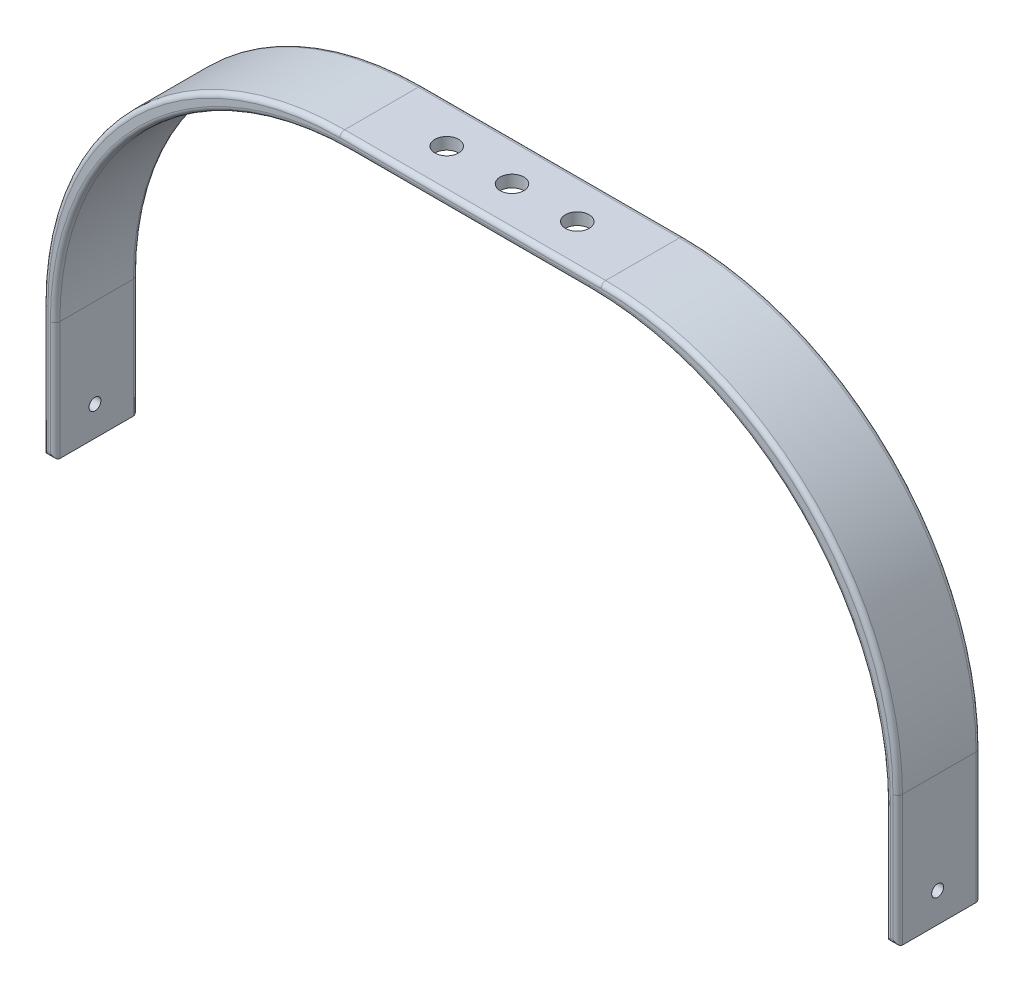
SolidWorks part; units mm, degrees
ref_plane "Front Plane" through (0, 0, 0) normal (0, 0, 1) x (1, 0, 0)
ref_plane "Top Plane" through (0, 0, 0) normal (0, 1, 0) x (1, 0, 0)
ref_plane "Right Plane" through (0, 0, 0) normal (1, 0, 0) x (0, 0, -1)
sketch "Sketch1" plane through (0, 0, 0) normal (0, 0, 1) x (1, 0, 0)
  line L0 (-110, 0) -> (90, 0)
  line L1 (340, -250) -> (340, -350)
  line L2 (-360, -250) -> (-360, -350)
  line L3 (-360, -350) -> (-370, -350)
  line L4 (-370, -350) -> (-370, -240)
  line L5 (-120, 10) -> (100, 10)
  line L6 (350, -240) -> (350, -350)
  line L7 (350, -350) -> (340, -350)
  arc A0 (100, 10) -> (350, -240) centre (100, -240) cw
  arc A1 (90, 0) -> (340, -250) centre (90, -250) cw
  arc A2 (-110, 0) -> (-360, -250) centre (-110, -250) ccw
  arc A3 (-370, -240) -> (-120, 10) centre (-120, -240) cw
  point P13 (340, 0)
  point P16 (-360, 0)
  dimension "D8" = 250
  dimension "D1" = 350
  dimension "D2" = 700
  dimension "D3" = 350
  dimension "D4" = 10
  dimension "D5" = 10
  dimension "D6" = 10
  dimension "D7" = 350
extrude "Boss-Extrude1" add sketch "Sketch1" along normal blind 70
sketch "Sketch2" plane through (350, 0, 0) normal (1, 0, 0) x (0, 0, -1)
  line L0 (-70, -350) -> (0, -350) construction
  circle A0 centre (-36.3899, -325) radius 5
  dimension "D1" = 10
  dimension "D2" = 25
extrude "Cut-Extrude1" cut sketch "Sketch2" against normal blind 816
sketch "Sketch3" plane through (0, 10, 0) normal (0, 1, 0) x (1, 0, 0)
  line L0 (-120, -35) -> (100, -35) construction
  line L1 (-120, -70) -> (-120, 0) construction
  line L2 (100, -70) -> (100, 0) construction
  circle A0 centre (-65, -35) radius 10
  circle A1 centre (-10, -35) radius 10
  circle A2 centre (45, -35) radius 10
  dimension "D1" = 20
  dimension "D2" = 55
  dimension "D3" = 3
extrude "Cut-Extrude2" cut sketch "Sketch3" against normal blind 143
fillet "Fillet1" radius 4 24 edges at (-10, 10, 0) (-296.7767, -63.2233, 0) (-370, -295, 0) (-365, -350, 0) (-360, -300, 0) (-286.7767, -73.2233, 0) (-10, 0, 0) (266.7767, -73.2233, 0) (340, -300, 0) (345, -350, 0) (350, -295, 0) (276.7767, -63.2233, 0) (350, -295, 70) (345, -350, 70) (340, -300, 70) (266.7767, -73.2233, 70) (-10, 0, 70) (-286.7767, -73.2233, 70) (-360, -300, 70) (-365, -350, 70) (-370, -295, 70) (-296.7767, -63.2233, 70) (-10, 10, 70) (276.7767, -63.2233, 70)
